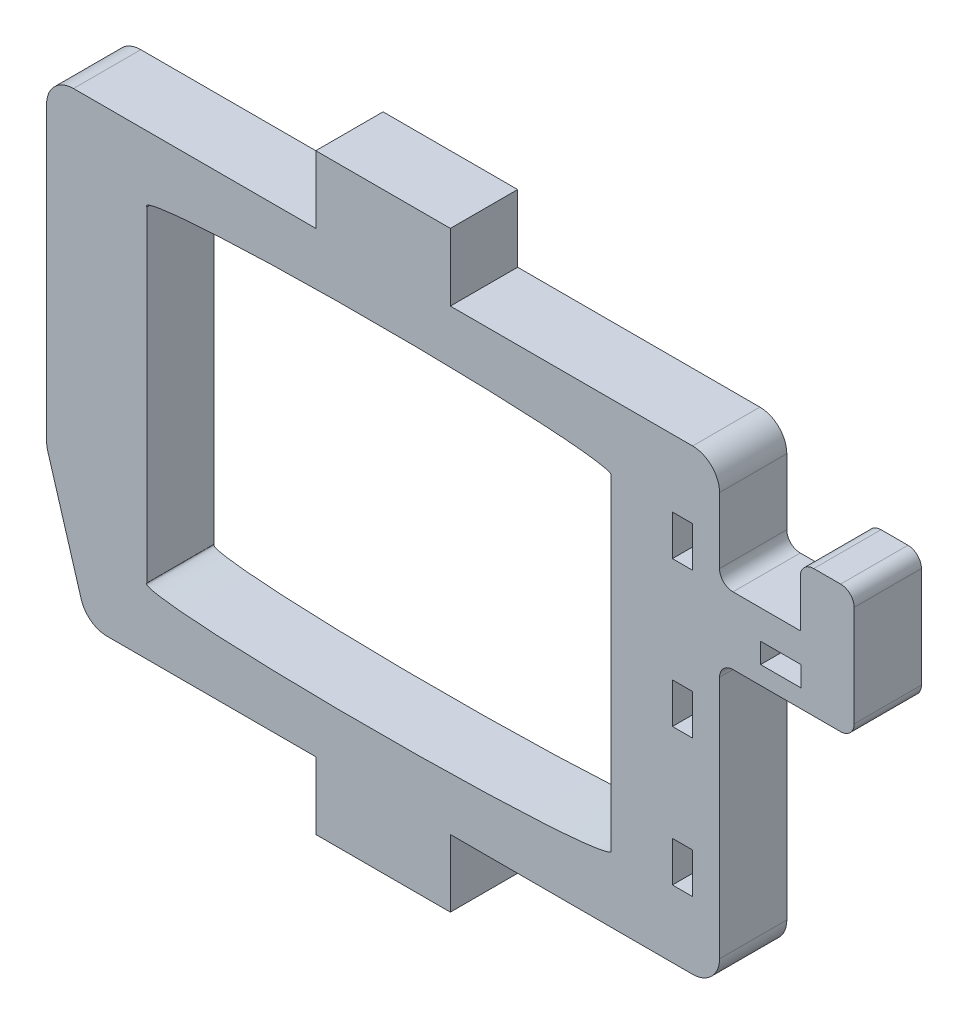
SolidWorks part; units mm, degrees
material "Acrílico (médio-alto impacto)"
ref_plane "Plano frontal" through (0, 0, 0) normal (0, 0, 1) x (1, 0, 0)
ref_plane "Plano superior" through (0, 0, 0) normal (0, 1, 0) x (1, 0, 0)
ref_plane "Plano direito" through (0, 0, 0) normal (1, 0, 0) x (0, 0, -1)
sketch "Esboço1" plane through (0, 0, 0) normal (0, 0, 1) x (1, 0, 0)
  line L0 (20, 34) -> (20, 0) construction
  line L1 (-5, 0) -> (15, 0)
  line L2 (-5, 0) -> (-5, 34)
  line L3 (-5, 34) -> (15, 34)
  line L4 (45, 0) -> (45, 34)
  line L5 (-5, 17) -> (45, 17) construction
  line L6 (15, -5) -> (20, 0) construction
  line L7 (15, 34) -> (15, 39)
  line L8 (15, 39) -> (25, 39)
  line L9 (25, 34) -> (25, 39)
  line L10 (20, 34) -> (25, 39) construction
  line L11 (15, 39) -> (20, 34) construction
  line L12 (20, 0) -> (25, -5) construction
  line L13 (25, 0) -> (25, -5)
  line L14 (15, -5) -> (25, -5)
  line L15 (15, 0) -> (15, -5)
  line L16 (25, 34) -> (45, 34)
  line L17 (25, 0) -> (45, 0)
  point P4 (20, 17)
  dimension "D1" = 34
  dimension "D2" = 50
  dimension "D3" = 5
  dimension "D4" = 10
extrude "Ressalto-extrusão1" add sketch "Esboço1" along normal blind 5
sketch "Esboço2" plane through (0, 0, 5) normal (0, 0, 1) x (1, 0, 0)
  line L0 (-5, 34) -> (45, 0) construction
  line L1 (45, 34) -> (-5, 0) construction
  line L2 (-5, 17) -> (45, 17) construction
  line L4 (2.4464, 4.9) -> (2.4464, 29.1)
  line L6 (36.9464, 4.9) -> (36.9464, 29.1)
  line L9 (-5, 34) -> (-5, 0) construction
  line L10 (45, 0) -> (45, 34) construction
  ellipse E0 centre (19.6846, 29.1262) end of major axis (36.9464, 29.1) minor radius 1 (36.9464, 29.1) -> (2.4464, 29.1) ccw
  ellipse E1 centre (19.6846, 4.8738) end of major axis (36.9464, 4.9) minor radius 1 (36.9464, 4.9) -> (2.4464, 4.9) cw
  point P8 (20, 17)
  dimension "D1" = 34.5
  dimension "D2" = 24.2
  dimension "D3" = 1
  dimension "D4" = 24.2
extrude "Corte-extrusão1" cut sketch "Esboço2" against normal through all
fillet "Filete1" radius 2 3 edges at (45, 0, 2.5) (45, 34, 2.5) (-5, 34, 2.5)
sketch "Esboço3" plane through (0, 0, 5) normal (0, 0, 1) x (1, 0, 0)
  line L0 (-5, 10) -> (-2, 0)
  line L1 (-5, 32) -> (-5, 0) construction
  line L2 (-5, 0) -> (15, 0) construction
  line L3 (-2, 0) -> (-5, 0)
  line L4 (-5, 0) -> (-5, 10)
  dimension "D1" = 3
  dimension "D2" = 10
extrude "Corte-extrusão2" cut sketch "Esboço3" against normal through all
fillet "Filete2" radius 2 2 edges at (-5, 10, 2.5) (-2, 0, 2.5)
sketch "Esboço4" plane through (0, 0, 0) normal (0, 0, -1) x (-1, 0, 0)
  line L0 (-43, 34) -> (-25, 34) construction
  line L1 (-25, 0) -> (-43, 0) construction
  line L12 (-43, 34) -> (-43, 0) construction
  line B0 (-43, 29) -> (-41.5, 29)
  line B1 (-43, 29) -> (-43, 26)
  line B2 (-43, 26) -> (-41.5, 26)
  line B3 (-41.5, 29) -> (-41.5, 26)
  line B4 (-43, 18.1995) -> (-41.5, 18.1995)
  line B5 (-43, 18.1995) -> (-43, 15.1995)
  line B6 (-43, 15.1995) -> (-41.5, 15.1995)
  line B7 (-41.5, 18.1995) -> (-41.5, 15.1995)
  line B8 (-43, 8) -> (-41.5, 8)
  line B9 (-43, 8) -> (-43, 5)
  line B10 (-43, 5) -> (-41.5, 5)
  line B11 (-41.5, 8) -> (-41.5, 5)
  dimension "D1" = 5
  dimension "D2" = 5
sketch_block_instance "Bloco1-1"
sketch_block "Bloco1" parameters "D1"=1.5, "D2"=3
sketch_block_instance "Bloco1-2"
sketch_block_instance "Bloco1-3"
extrude "Corte-extrusão3" cut sketch "Esboço4" against normal through all
sketch "Esboço5" plane through (45, 0, 0) normal (1, 0, 0) x (0, 0, -1)
  line L0 (-5, 2) -> (-5, 32) construction
  line L1 (-5, 26.1113) -> (0, 26.1113)
  line L2 (-5, 26.1113) -> (-5, 21.1113)
  line L3 (-5, 21.1113) -> (0, 21.1113)
  line L4 (0, 26.1113) -> (0, 21.1113)
  line L5 (0, 2) -> (0, 32) construction
  dimension "D1" = 5
  dimension "D2" = 5
extrude "Ressalto-extrusão2" add sketch "Esboço5" along normal blind 10
sketch "Esboço6" plane through (0, 26.1113, 0) normal (0, 1, 0) x (1, 0, 0)
  line L0 (55, 0) -> (45, 0) construction
  line L1 (55, -5) -> (51, -5)
  line L2 (55, -5) -> (55, 0)
  line L3 (55, 0) -> (51, 0)
  line L4 (51, -5) -> (51, 0)
  dimension "D1" = 4
extrude "Ressalto-extrusão3" add sketch "Esboço6" along normal blind 4.5
sketch "Esboço7" plane through (0, 0, 5) normal (0, 0, 1) x (1, 0, 0)
  line L3 (48.0504, 23.9576) -> (51.0504, 23.9576)
  line L4 (48.0504, 23.9576) -> (48.0504, 22.4576)
  line L5 (48.0504, 22.4576) -> (51.0504, 22.4576)
  line L6 (51.0504, 23.9576) -> (51.0504, 22.4576)
  dimension "D1" = 3
  dimension "D2" = 1.5
extrude "Corte-extrusão4" cut sketch "Esboço7" against normal through all
fillet "Filete3" radius 1 5 edges at (45, 21.1113, 2.5) (55, 21.1113, 2.5) (51, 30.6113, 2.5) (55, 30.6113, 2.5) (45, 26.1113, 2.5)
